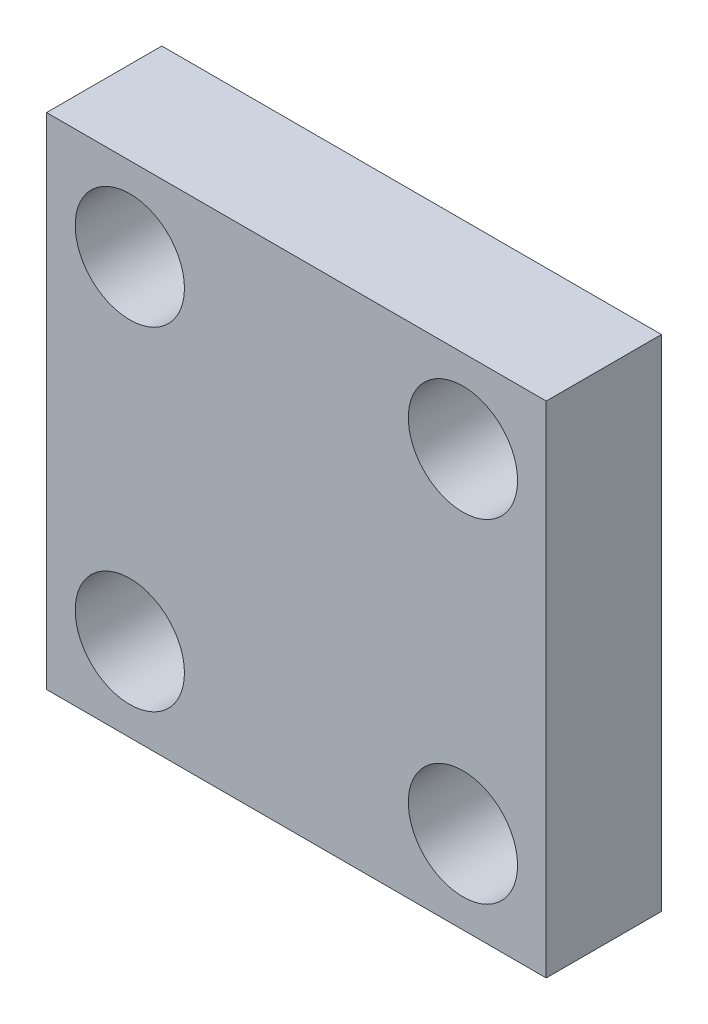
SolidWorks part; units mm, degrees
ref_plane "Front Plane" through (0, 0, 0) normal (0, 0, 1) x (1, 0, 0)
ref_plane "Top Plane" through (0, 0, 0) normal (0, 1, 0) x (1, 0, 0)
ref_plane "Right Plane" through (0, 0, 0) normal (1, 0, 0) x (0, 0, -1)
sketch "Sketch1" plane through (0, 0, 0) normal (0, 0, 1) x (1, 0, 0)
  line L0 (9.525, 19.05) -> (9.525, 0) construction
  line L1 (0, 0) -> (19.05, 0)
  line L2 (0, 0) -> (0, 19.05)
  line L3 (0, 19.05) -> (19.05, 19.05)
  line L4 (19.05, 0) -> (19.05, 19.05)
  line L5 (0, 9.525) -> (19.05, 9.525) construction
  circle A0 centre (3.175, 3.175) radius 2.0828
  circle A1 centre (3.175, 15.875) radius 2.0828
  circle A2 centre (15.875, 15.875) radius 2.0828
  circle A3 centre (15.875, 3.175) radius 2.0828
  dimension "D1" = 4.1656
  dimension "D2" = 12.7
  dimension "D3" = 12.7
  dimension "D4" = 19.05
  dimension "D5" = 19.05
  dimension "D6" = 12.7
  dimension "D7" = 12.7
extrude "Boss-Extrude1" add sketch "Sketch1" along normal blind 4.3942
